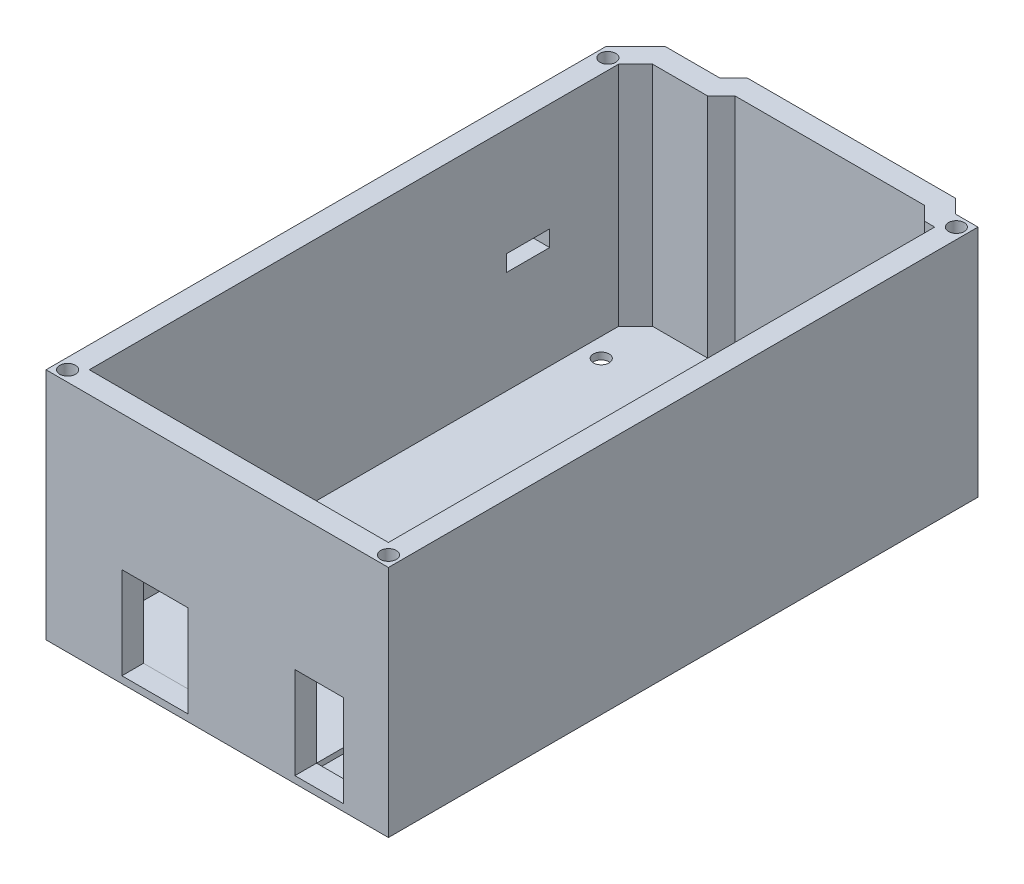
SolidWorks part; units mm, degrees
ref_plane "Front" through (0, 0, 0) normal (0, 0, 1) x (1, 0, 0)
ref_plane "Top" through (0, 0, 0) normal (0, 1, 0) x (1, 0, 0)
ref_plane "Right" through (0, 0, 0) normal (1, 0, 0) x (0, 0, -1)
sketch "Sketch2" plane through (0, 0, 0) normal (0, 1, 0) x (1, 0, 0)
  line L0 (52.07, 99.06) -> (49.53, 101.6)
  line L1 (0, 0) -> (53.34, 0)
  line L2 (0, 0) -> (0, 96.52)
  line L3 (2.54, 99.06) -> (12.7, 99.06)
  line L4 (53.34, 0) -> (53.34, 99.06)
  line L5 (49.53, 101.6) -> (15.24, 101.6)
  line L6 (15.24, 101.6) -> (12.7, 99.06)
  line L7 (0, 96.52) -> (2.54, 99.06)
  line L8 (52.07, 99.06) -> (53.34, 99.06)
  circle A0 centre (50.8, 13.97) radius 1.45
  circle A1 centre (2.54, 15.24) radius 1.45
  circle A2 centre (50.8, 96.52) radius 1.45
  circle A3 centre (2.54, 90.17) radius 1.45
  dimension "D9" = 2.9
  dimension "D1" = 2.54
  dimension "D2" = 2.54
  dimension "D3" = 2.54
  dimension "D4" = 34.29
  dimension "D5" = 2.54
  dimension "D6" = 1.27
  dimension "D7" = 10.16
  dimension "D8" = 101.6
  dimension "D10" = 2.54
  dimension "D11" = 2.54
  dimension "D12" = 13.97
  dimension "D13" = 15.24
  dimension "D14" = 90.17
  dimension "D15" = 2.54
  dimension "D16" = 2.54
  dimension "D17" = 2.54
extrude "Boss-Extrude1" add sketch "Sketch2" along normal blind 1.27
sketch "Sketch3" plane through (0, 0, 0) normal (0, -1, 0) x (1, 0, 0)
  line L0 (49.9442, -102.6) -> (52.4842, -100.06)
  line L1 (52.4842, -100.06) -> (54.34, -100.06)
  line L2 (54.34, -100.06) -> (54.34, 1)
  line L3 (54.34, 1) -> (-1, 1)
  line L4 (-1, 1) -> (-1, -96.9342)
  line L5 (-1, -96.9342) -> (2.1258, -100.06)
  line L6 (2.1258, -100.06) -> (12.2858, -100.06)
  line L7 (12.2858, -100.06) -> (14.8258, -102.6)
  line L8 (14.8258, -102.6) -> (49.9442, -102.6)
  line L9 (0, 0) -> (0, -96.52)
  line L10 (0, -96.52) -> (2.54, -99.06)
  line L11 (2.54, -99.06) -> (12.7, -99.06)
  line L12 (12.7, -99.06) -> (15.24, -101.6)
  line L13 (15.24, -101.6) -> (49.53, -101.6)
  line L14 (49.53, -101.6) -> (52.07, -99.06)
  line L15 (52.07, -99.06) -> (53.34, -99.06)
  line L16 (53.34, -99.06) -> (53.34, 0)
  line L17 (53.34, 0) -> (0, 0)
  line L18 (0, 0) -> (0, -96.52)
  line L19 (0, -96.52) -> (2.54, -99.06)
  line L20 (2.54, -99.06) -> (12.7, -99.06)
  line L21 (12.7, -99.06) -> (15.24, -101.6)
  line L22 (15.24, -101.6) -> (49.53, -101.6)
  line L23 (49.53, -101.6) -> (52.07, -99.06)
  line L24 (52.07, -99.06) -> (53.34, -99.06)
  line L25 (53.34, -99.06) -> (53.34, 0)
  line L26 (53.34, 0) -> (0, 0)
  dimension "D1" = 0
  dimension "D2" = 1
extrude "Boss-Extrude2" add sketch "Sketch3" against normal up to surface (1.27 mm away) up to face at (26.5289, 1.27, -77.3289)
sketch "Sketch4" plane through (0, 0, 0) normal (0, -1, 0) x (1, 0, 0)
  line L1 (-5, 5) -> (-5, -98.5911)
  line L2 (-5, -98.5911) -> (0.4689, -104.06)
  line L3 (0.4689, -104.06) -> (10.6289, -104.06)
  line L4 (10.6289, -104.06) -> (13.1689, -106.6)
  line L5 (13.1689, -106.6) -> (51.6011, -106.6)
  line L6 (51.6011, -106.6) -> (54.1411, -104.06)
  line L7 (54.1411, -104.06) -> (58.34, -104.06)
  line L8 (58.34, -104.06) -> (58.34, 5)
  line L9 (14.8258, -102.6) -> (49.9442, -102.6)
  line L10 (49.9442, -102.6) -> (52.4842, -100.06)
  line L11 (52.4842, -100.06) -> (54.34, -100.06)
  line L12 (54.34, -100.06) -> (54.34, 1)
  line L13 (54.34, 1) -> (-1, 1)
  line L14 (-1, 1) -> (-1, -96.9342)
  line L15 (-1, -96.9342) -> (2.1258, -100.06)
  line L16 (2.1258, -100.06) -> (12.2858, -100.06)
  line L17 (12.2858, -100.06) -> (14.8258, -102.6)
  line L18 (14.8258, -102.6) -> (49.9442, -102.6)
  line L19 (49.9442, -102.6) -> (52.4842, -100.06)
  line L20 (52.4842, -100.06) -> (54.34, -100.06)
  line L21 (54.34, -100.06) -> (54.34, 1)
  line L22 (54.34, 1) -> (-1, 1)
  line L23 (-1, 1) -> (-1, -96.9342)
  line L24 (-1, -96.9342) -> (2.1258, -100.06)
  line L25 (2.1258, -100.06) -> (12.2858, -100.06)
  line L26 (12.2858, -100.06) -> (14.8258, -102.6)
  line L27 (58.34, 5) -> (-5, 5)
  dimension "D1" = 0
  dimension "D2" = 4
extrude "Boss-Extrude3" add sketch "Sketch4" along direction (0, 1, 0) on the side against the normal offset from surface (18.27 mm away) 17 separate body
sketch "Sketch5" plane through (0, 18.27, 0) normal (0, 1, 0) x (1, 0, 0)
  line L0 (-1, -1) -> (54.34, -1) construction
  line L1 (9.04, -1) -> (21.24, -1)
  line L2 (9.04, -1) -> (9.04, -5)
  line L3 (9.04, -5) -> (21.24, -5)
  line L4 (21.24, -1) -> (21.24, -5)
  line L5 (-5, -5) -> (58.34, -5) construction
  line L7 (41.04, -1) -> (50.04, -1)
  line L8 (41.04, -1) -> (41.04, -5)
  line L9 (41.04, -5) -> (50.04, -5)
  line L10 (50.04, -1) -> (50.04, -5)
  circle A0 centre (2.54, 15.24) radius 1.45 construction
  dimension "D1" = 12.2
  dimension "D2" = 9
  dimension "D3" = 41
  dimension "D4" = 6.5
extrude "Cut-Extrude1" cut sketch "Sketch5" against normal up to surface (17 mm away) up to face at (50.8, 1.27, -12.52)
sketch "Sketch6" plane through (0, 18.27, 0) normal (0, 1, 0) x (1, 0, 0)
  line L1 (9.04, -1) -> (50.04, -1)
  line L3 (9.04, -5) -> (50.04, -5)
  line L22 (-5, -5) -> (9.04, -5)
  line L23 (9.04, -5) -> (9.04, -1)
  line L24 (9.04, -1) -> (-1, -1)
  line L25 (-1, -1) -> (-1, 96.9342)
  line L26 (-1, 96.9342) -> (2.1258, 100.06)
  line L27 (2.1258, 100.06) -> (12.2858, 100.06)
  line L28 (12.2858, 100.06) -> (14.8258, 102.6)
  line L29 (14.8258, 102.6) -> (49.9442, 102.6)
  line L30 (49.9442, 102.6) -> (52.4842, 100.06)
  line L31 (52.4842, 100.06) -> (54.34, 100.06)
  line L32 (54.34, 100.06) -> (54.34, -1)
  line L33 (54.34, -1) -> (50.04, -1)
  line L34 (50.04, -1) -> (50.04, -5)
  line L35 (50.04, -5) -> (58.34, -5)
  line L36 (58.34, -5) -> (58.34, 104.06)
  line L37 (58.34, 104.06) -> (54.1411, 104.06)
  line L38 (54.1411, 104.06) -> (51.6011, 106.6)
  line L39 (51.6011, 106.6) -> (13.1689, 106.6)
  line L40 (13.1689, 106.6) -> (10.6289, 104.06)
  line L41 (10.6289, 104.06) -> (0.4689, 104.06)
  line L42 (0.4689, 104.06) -> (-5, 98.5911)
  line L43 (-5, 98.5911) -> (-5, -5)
  line L44 (-5, -5) -> (9.04, -5)
  line L46 (9.04, -1) -> (-1, -1)
  line L47 (-1, -1) -> (-1, 96.9342)
  line L48 (-1, 96.9342) -> (2.1258, 100.06)
  line L49 (2.1258, 100.06) -> (12.2858, 100.06)
  line L50 (12.2858, 100.06) -> (14.8258, 102.6)
  line L51 (14.8258, 102.6) -> (49.9442, 102.6)
  line L52 (49.9442, 102.6) -> (52.4842, 100.06)
  line L53 (52.4842, 100.06) -> (54.34, 100.06)
  line L54 (54.34, 100.06) -> (54.34, -1)
  line L55 (54.34, -1) -> (50.04, -1)
  line L57 (50.04, -5) -> (58.34, -5)
  line L58 (58.34, -5) -> (58.34, 104.06)
  line L59 (58.34, 104.06) -> (54.1411, 104.06)
  line L60 (54.1411, 104.06) -> (51.6011, 106.6)
  line L61 (51.6011, 106.6) -> (13.1689, 106.6)
  line L62 (13.1689, 106.6) -> (10.6289, 104.06)
  line L63 (10.6289, 104.06) -> (0.4689, 104.06)
  line L64 (0.4689, 104.06) -> (-5, 98.5911)
  line L65 (-5, 98.5911) -> (-5, -5)
  dimension "D1" = 0
extrude "Boss-Extrude4" add sketch "Sketch6" along normal blind 25
sketch "Sketch7" plane through (0, 43.27, 0) normal (0, 1, 0) x (1, 0, 0)
  line L0 (26.67, -1) -> (26.67, -5) construction
  line L1 (-1, -1) -> (54.34, -1) construction
  line L2 (-5, -5) -> (58.34, -5) construction
  line L3 (54.34, 49.53) -> (58.34, 49.53) construction
  line L4 (54.34, -1) -> (54.34, 100.06) construction
  line L5 (58.34, -5) -> (58.34, 104.06) construction
  line L6 (-1, 47.9671) -> (-5, 47.9671) construction
  line L7 (-1, 96.9342) -> (-1, -1) construction
  line L8 (-5, 98.5911) -> (-5, -5) construction
  line L9 (54.1411, 104.06) -> (54.1411, 100.06) construction
  line L10 (54.34, 100.06) -> (52.4842, 100.06) construction
  circle A0 centre (-3, -3) radius 1.45
  circle A1 centre (56.34, -3) radius 1.45
  circle A2 centre (56.34, 102.06) radius 1.45
  circle A3 centre (-3, 96.9342) radius 1.45
  point P8 (54.1411, 102.06)
  point P10 (26.67, -3)
  point P23 (56.34, 49.53)
  point P30 (-3, 47.9671)
  dimension "D1" = 2.9
extrude "Cut-Extrude2" cut sketch "Sketch7" against normal blind 12
sketch "Sketch8" plane through (-5, 0, 0) normal (-1, 0, 0) x (0, 0, 1)
  line L1 (-84.1734, 23.2627) -> (-76.1734, 23.2627)
  line L2 (-84.1734, 23.2627) -> (-84.1734, 20.2627)
  line L3 (-84.1734, 20.2627) -> (-76.1734, 20.2627)
  line L4 (-76.1734, 23.2627) -> (-76.1734, 20.2627)
  dimension "D1" = 8
  dimension "D2" = 3
extrude "Cut-Extrude3" cut sketch "Sketch8" against normal up to next (4 mm away)
sketch "Sketch9" plane through (0, 1.27, 0) normal (0, 1, 0) x (1, 0, 0)
  line L1 (41.04, -1) -> (52.8673, -1)
  line L2 (41.04, -1) -> (41.04, 13.419)
  line L3 (41.04, 13.419) -> (52.8673, 13.419)
  line L4 (52.8673, -1) -> (52.8673, 13.419)
  point P5 (52.8673, 13.419)
extrude "Cut-Extrude4" cut sketch "Sketch9" against normal blind 1
